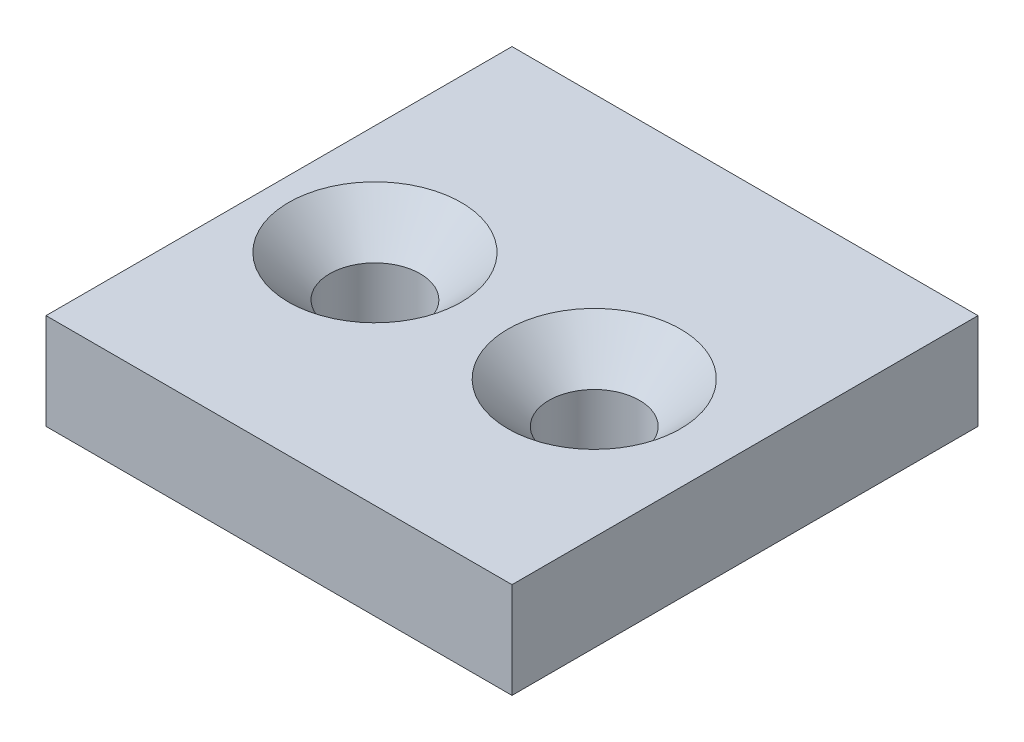
SolidWorks part; units mm, degrees
ref_plane "Front Plane" through (0, 0, 0) normal (0, 0, 1) x (1, 0, 0)
ref_plane "Top Plane" through (0, 0, 0) normal (0, 1, 0) x (1, 0, 0)
ref_plane "Right Plane" through (0, 0, 0) normal (1, 0, 0) x (0, 0, -1)
sketch "Sketch3" plane through (0, 0, 0) normal (0, 1, 0) x (1, 0, 0)
  line L1 (0, 0) -> (34, 0)
  line L2 (0, 0) -> (0, 34)
  line L3 (0, 34) -> (34, 34)
  line L4 (34, 0) -> (34, 34)
  dimension "D1" = 34
  dimension "D2" = 34
extrude "Boss-Extrude2" add sketch "Sketch3" along normal blind 7
hole_wizard "CSK for M6 Flat Head Machine Screw1" positions "Sketch8" profile "Sketch9" countersink size "M6" standard "ANSI Metric" end condition through all
sketch "Sketch8" plane through (0, 7, 0) normal (0, 1, 0) x (1, 0, 0)
  line L0 (0, 34) -> (0, 0) construction
  line L1 (0, 0) -> (34, 0) construction
  point P0 (8, 16)
  point P2 (24, 16)
  dimension "D1" = 16
  dimension "D2" = 8
  dimension "D3" = 16
sketch "Sketch9" plane through (8, 7, -16) normal (1, 0, 0) x (0, 0, 1)
  line L0 (0, 0) -> (0, 7)
  line L1 (0, 7) -> (3.3, 7)
  line L2 (3.3, 7) -> (3.3, 3)
  line L3 (3.3, 3) -> (6.3, 0)
  line L5 (6.3, 0) -> (0, 0)
  line L6 (-3.3, 3) -> (-6.3, 0) construction
  line L11 (0, -6.35) -> (0, 107.95) construction
  dimension "Thru Hole Dia." = 6.6
  dimension "Thru Hole Depth" = 7
  dimension "Near C'Sink Dia." = 12.6
  dimension "Near C'Sink Angle" = 90
